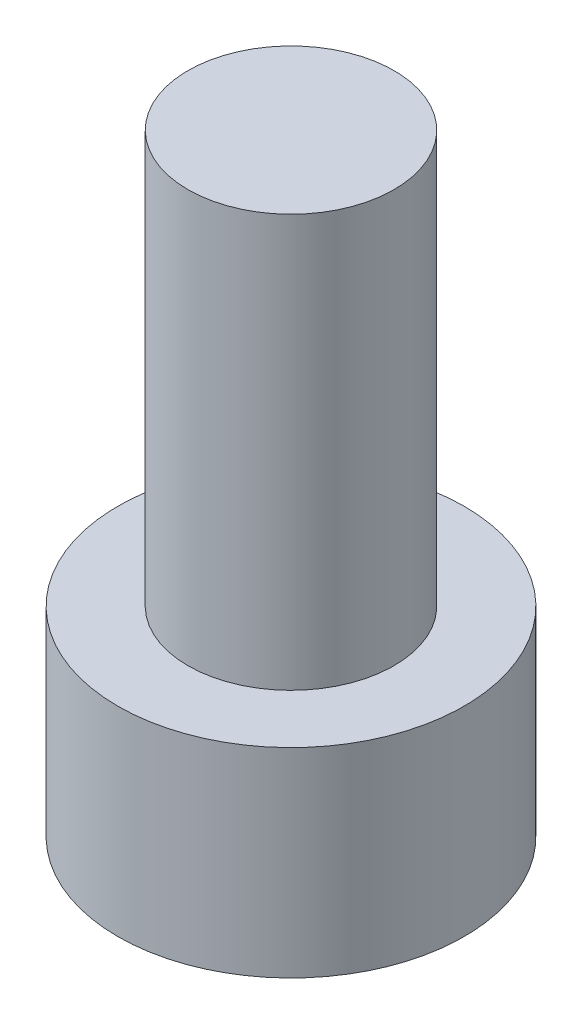
SolidWorks part; units mm, degrees
ref_plane "前视基准面" through (0, 0, 0) normal (0, 0, 1) x (1, 0, 0)
ref_plane "上视基准面" through (0, 0, 0) normal (0, 1, 0) x (1, 0, 0)
ref_plane "右视基准面" through (0, 0, 0) normal (1, 0, 0) x (0, 0, -1)
sketch "草图1" plane through (0, 0, 0) normal (0, 1, 0) x (1, 0, 0)
  circle A0 centre (0, 0) radius 4.2
extrude "凸台-拉伸1" add sketch "草图1" along normal blind 4.84
sketch "草图2" plane through (0, 4.84, 0) normal (0, 1, 0) x (1, 0, 0)
  circle A0 centre (0, 0) radius 2.5
extrude "凸台-拉伸2" add sketch "草图2" along normal blind 10
sketch "草图3" plane through (0, 0, 0) normal (0, -1, 0) x (1, 0, 0)
  line L1 (2.3, 0) -> (1.15, 1.9919)
  line L2 (1.15, 1.9919) -> (-1.15, 1.9919)
  line L3 (-1.15, 1.9919) -> (-2.3, 0)
  line L4 (-2.3, 0) -> (-1.15, -1.9919)
  line L5 (-1.15, -1.9919) -> (1.15, -1.9919)
  line L6 (1.15, -1.9919) -> (2.3, 0)
  circle A0 centre (0, 0) radius 1.9919 construction
extrude "切除-拉伸1" cut sketch "草图3" against normal blind 3.4
